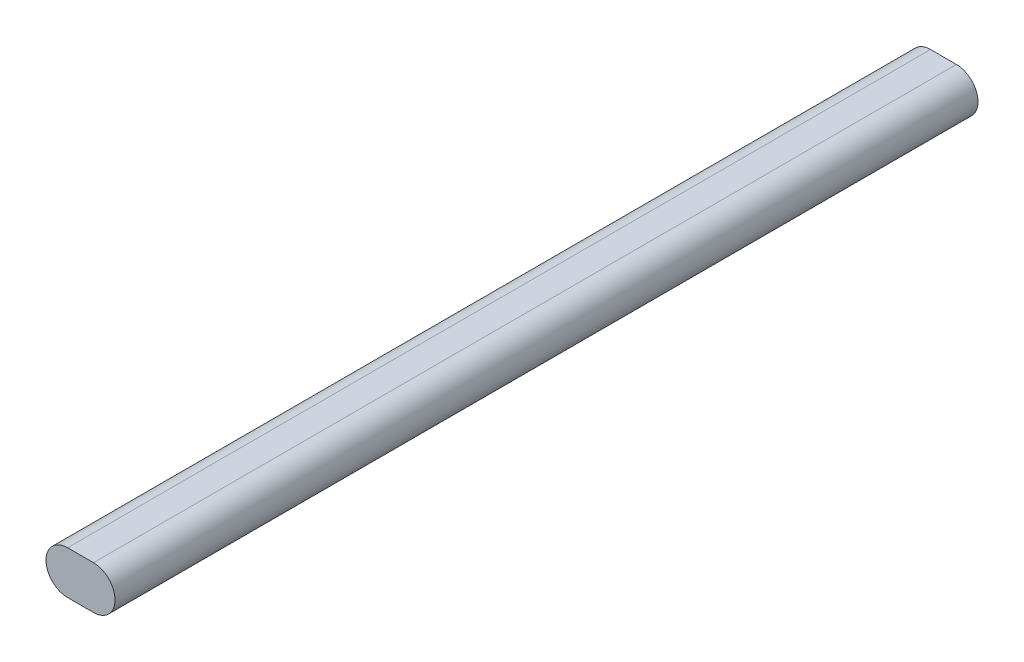
SolidWorks part; units mm, degrees
ref_plane "Front Plane" through (0, 0, 0) normal (0, 0, 1) x (1, 0, 0)
ref_plane "Top Plane" through (0, 0, 0) normal (0, 1, 0) x (1, 0, 0)
ref_plane "Right Plane" through (0, 0, 0) normal (1, 0, 0) x (0, 0, -1)
sketch "Sketch1" plane through (0, 0, 0) normal (0, 0, 1) x (1, 0, 0)
  line L0 (-7.5, 0) -> (7.5, 0) construction
  line L1 (-7.5, 12.5) -> (7.5, 12.5)
  line L2 (-7.5, -12.5) -> (7.5, -12.5)
  arc A0 (-7.5, 12.5) -> (-7.5, -12.5) centre (-7.5, 0) ccw
  arc A1 (7.5, -12.5) -> (7.5, 12.5) centre (7.5, 0) ccw
  point P2 (0, 0)
  point P8 (-20, 0)
  point P9 (20, 0)
  dimension "D2" = 40
  dimension "D1" = 25
extrude "Boss-Extrude1" add sketch "Sketch1" along normal blind 500
